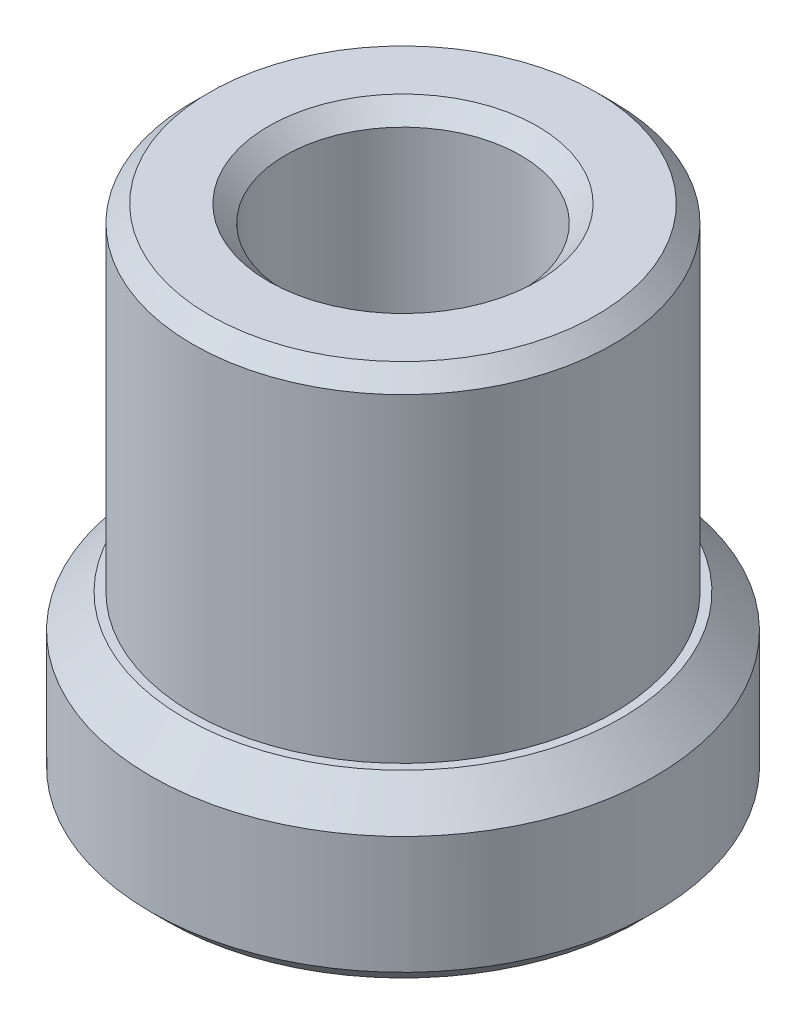
SolidWorks part; units mm, degrees
material "AISI 304"
ref_plane "Спереди" through (0, 0, 0) normal (0, 0, 1) x (1, 0, 0)
ref_plane "Сверху" through (0, 0, 0) normal (0, 1, 0) x (1, 0, 0)
ref_plane "Справа" through (0, 0, 0) normal (1, 0, 0) x (0, 0, -1)
sketch "Эскиз1" plane through (0, 0, 0) normal (0, 0, 1) x (1, 0, 0)
  line L0 (0, 30) -> (0, 0) construction
  line L1 (0, 0) -> (-15, 0)
  line L2 (-15, 0) -> (-15, 10)
  line L3 (-15, 10) -> (-12.5, 10)
  line L4 (-12.5, 10) -> (-12.5, 30)
  line L5 (-12.5, 30) -> (0, 30)
  line L6 (0, 30) -> (0, 0)
  dimension "D1" = 25
  dimension "D2" = 30
  dimension "D3" = 20
  dimension "D4" = 10
revolve "Повернуть1" add sketch "Эскиз1" angle 360 about L0
chamfer "Фаска1" distance 1 angle 45 2 edges at (0, 0, 15) (0, 30, 12.5)
chamfer "Фаска2" distance 2 angle 45 1 edges at (0, 10, 15)
hole_wizard "Отверстие обработанное метчиком M161" positions "Эскиз3" profile "Эскиз2" tap size "M16" standard "DIN"
sketch "Эскиз3" plane through (0, 0, 0) normal (0, -1, 0) x (-1, 0, 0)
  point P0 (0, 0)
sketch "Эскиз2" plane through (0, 0, 0) normal (1, 0, 0) x (0, 0, -1)
  line L0 (0, 0) -> (0, 54.0415)
  line L1 (0, 54.0415) -> (7, 50)
  line L2 (7, 50) -> (7, 0)
  line L5 (7, 0) -> (0, 0)
  line L10 (0, 54.0415) -> (-7, 50) construction
  line L11 (0, -6.35) -> (0, 107.95) construction
  dimension "Диаметр сверла" = 14
  dimension "Глубина сверла" = 50
  dimension "Угол заточки сверла" = 120
cosmetic thread "Отверстие резьбы1" parameters "D1"=30, "D2"=16
chamfer "Фаска3" distance 1 angle 45 2 edges at (0, 0, -7) (0, 30, 7)
